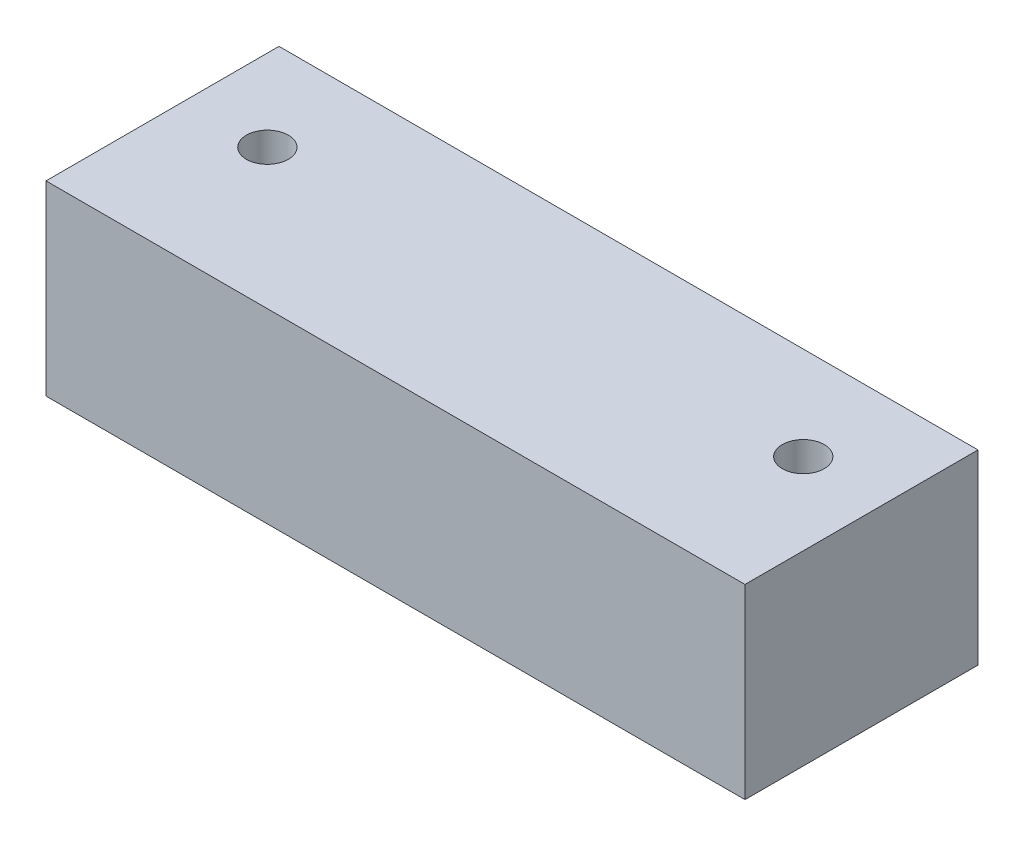
SolidWorks part; units mm, degrees
material "Plain Carbon Steel"
ref_plane "Front Plane" through (0, 0, 0) normal (0, 0, 1) x (1, 0, 0)
ref_plane "Top Plane" through (0, 0, 0) normal (0, 1, 0) x (1, 0, 0)
ref_plane "Right Plane" through (0, 0, 0) normal (1, 0, 0) x (0, 0, -1)
sketch "Sketch1" plane through (0, 0, 0) normal (0, 0, 1) x (1, 0, 0)
  line L0 (-150, -40) -> (150, -40)
  line L1 (-150, -40) -> (-150, 40)
  line L2 (150, -40) -> (150, 40)
  line L3 (-150, 40) -> (150, 40)
  line L4 (-150, -40) -> (150, 40) construction
  line L5 (150, -40) -> (-150, 40) construction
  point P2 (0, 0)
  dimension "D1" = 300
  dimension "D2" = 80
extrude "Boss-Extrude1" add sketch "Sketch1" along normal mid plane 100
sketch "Sketch2" plane through (0, 0, 0) normal (0, 1, 0) x (1, 0, 0)
  line L0 (-150, 10) -> (150, 10) construction
  line L1 (-150, -50) -> (-150, 50) construction
  line L2 (150, -50) -> (150, 50) construction
  line L3 (150, 50) -> (-150, 50) construction
  circle A0 centre (-115, 10) radius 9
  circle A1 centre (115, 10) radius 9
  dimension "D4" = 18
  dimension "D1" = 115
  dimension "D2" = 115
  dimension "D3" = 40
extrude "Cut-Extrude1" cut sketch "Sketch2" against normal through all and the other way through all
